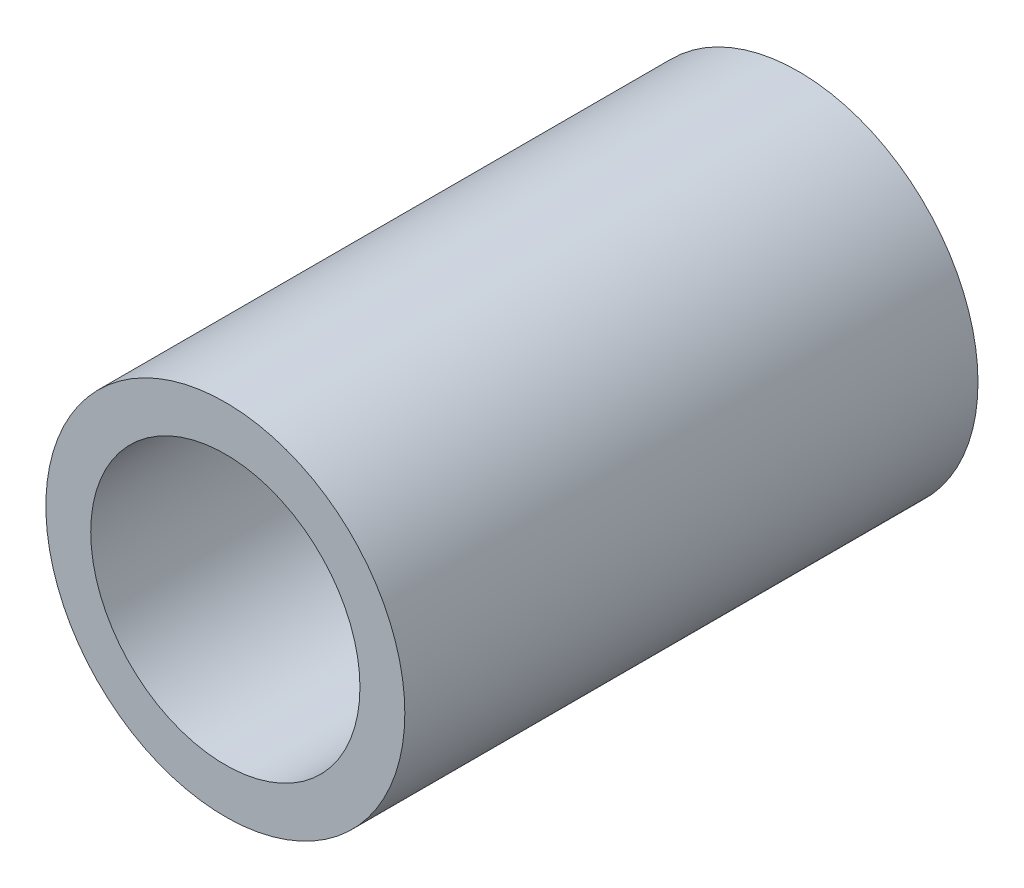
SolidWorks part; units mm, degrees
ref_plane "Front Plane" through (0, 0, 0) normal (0, 0, 1) x (1, 0, 0)
ref_plane "Top Plane" through (0, 0, 0) normal (0, 1, 0) x (1, 0, 0)
ref_plane "Right Plane" through (0, 0, 0) normal (1, 0, 0) x (0, 0, -1)
sketch "Sketch1" plane through (0, 0, 0) normal (0, 0, 1) x (1, 0, 0)
  line L0 (-38.1, 0) -> (38.1, 0) construction
  line L1 (0, -38.1) -> (0, 38.1) construction
  line L2 (0, 0) -> (0, 82.55) construction
  circle A0 centre (0, 0) radius 38.1
  circle A1 centre (0, 0) radius 28.575
  point P4 (0, 0)
  point P9 (0, 0)
  point P10 (28.575, 0)
  dimension "D1" = 57.15
  dimension "OD" = 76.2
  dimension "Wall Thickness" = 9.525
sketch "Sketch2" plane through (0, 0, 0) normal (1, 0, 0) x (0, 0, -1)
  line L0 (60.833, 38.1) -> (-60.833, 38.1) construction
  line L1 (0, 38.1) -> (0, -38.1) construction
  point P3 (26.797, 38.1)
  point P4 (0, 38.1)
  point P5 (-26.797, 38.1)
  dimension "D1" = 87.63
  dimension "D2" = 87.63
  dimension "Length" = 121.666
sketch "Sketch3" plane through (0, 0, 0) normal (0, 0, 1) x (1, 0, 0)
  line L0 (0, -38.1) -> (0, 38.1) construction
  circle A0 centre (0, 0) radius 38.1
  circle A1 centre (0, 0) radius 28.575
  circle A2 centre (0, 0) radius 28.575 construction
extrude "Boss-Extrude1" add sketch "Sketch3" along normal mid plane 121.666
equation "\"D1@Boss-Extrude1\" = \"Length@Sketch2\""
equation "\"D1@Sketch2\"=\"OD@Sketch1\"*1.15"
equation "\"D2@Sketch2\"=\"D1@Sketch2\""
